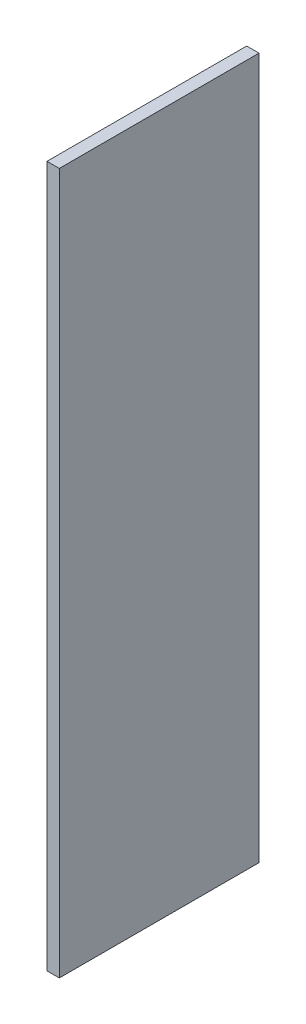
SolidWorks part; units mm, degrees
ref_plane "Front Plane" through (0, 0, 0) normal (0, 0, 1) x (1, 0, 0)
ref_plane "Top Plane" through (0, 0, 0) normal (0, 1, 0) x (1, 0, 0)
ref_plane "Right Plane" through (0, 0, 0) normal (1, 0, 0) x (0, 0, -1)
sketch "Sketch1" plane through (0, 0, 0) normal (1, 0, 0) x (0, 0, -1)
  line L1 (24.3921, -967.2196) -> (-267.6079, -967.2196)
  line L2 (24.3921, -967.2196) -> (24.3921, 57.7804)
  line L3 (24.3921, 57.7804) -> (-267.6079, 57.7804)
  line L4 (-267.6079, -967.2196) -> (-267.6079, 57.7804)
  line L5 (24.3921, -967.2196) -> (-267.6079, 57.7804) construction
  line L6 (24.3921, 57.7804) -> (-267.6079, -967.2196) construction
  point P0 (-121.6079, -454.7196)
  dimension "D1" = 292
  dimension "D2" = 1025
extrude "Boss-Extrude1" add sketch "Sketch1" along normal blind 18
equation "\"H_POLKI\"=1025"
equation "\"D2@Sketch1\"=\"H_POLKI\""
equation "\"DSP_WIDTH\"=18"
equation "\"D1@Boss-Extrude1\"=\"DSP_WIDTH\""
